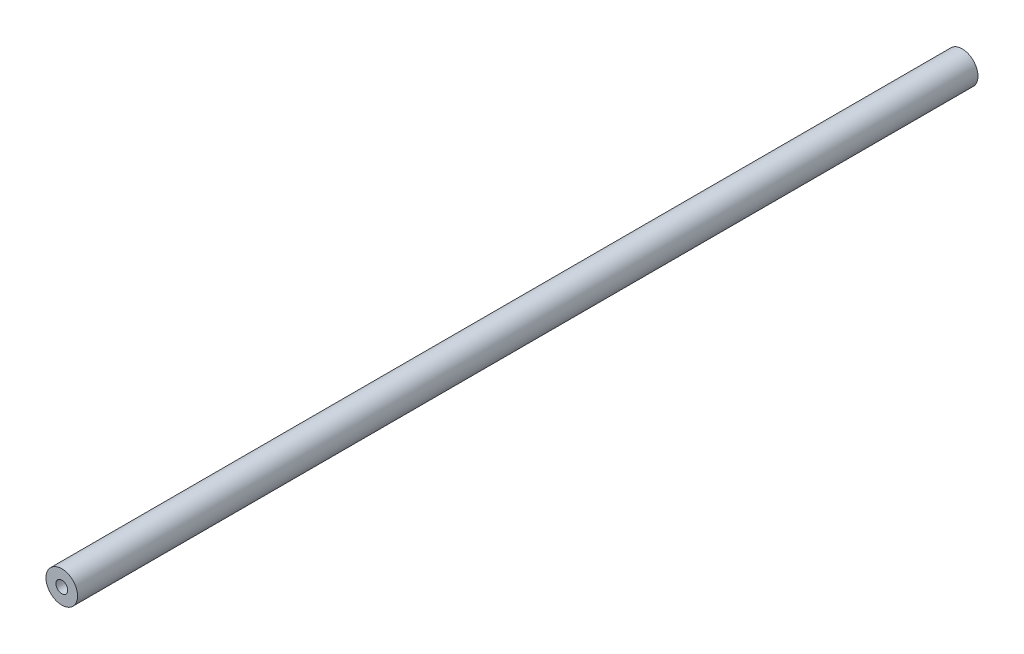
SolidWorks part; units mm, degrees
material "Cast Carbon Steel"
ref_plane "Front Plane" through (0, 0, 0) normal (0, 0, 1) x (1, 0, 0)
ref_plane "Top Plane" through (0, 0, 0) normal (0, 1, 0) x (1, 0, 0)
ref_plane "Right Plane" through (0, 0, 0) normal (1, 0, 0) x (0, 0, -1)
sketch "Sketch1" plane through (0, 0, 0) normal (0, 0, 1) x (1, 0, 0)
  circle A0 centre (0, 0) radius 12.7
  circle A1 centre (0, 0) radius 4.7625
  dimension "D1" = 25.4
  dimension "D2" = 7.9375
extrude "Boss-Extrude1" add sketch "Sketch1" along normal blind 723.9
